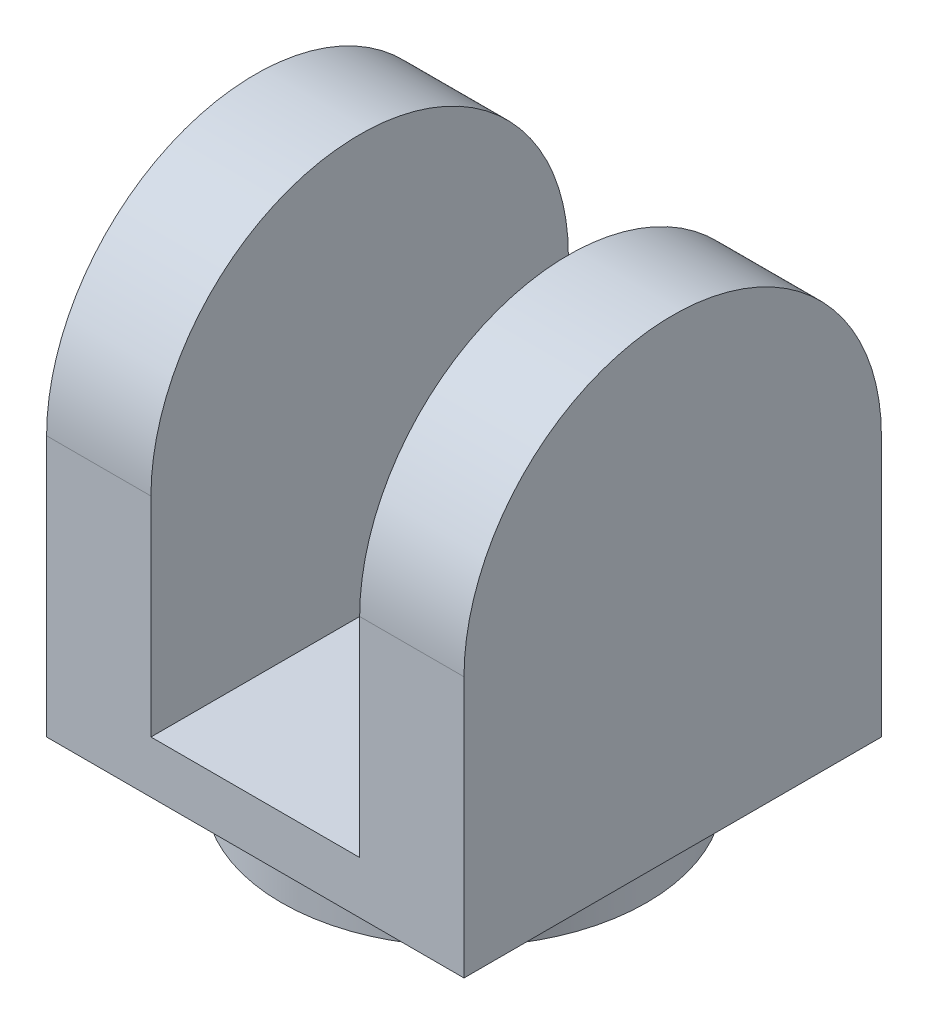
SolidWorks part; units mm, degrees
ref_plane "前视基准面" through (0, 0, 0) normal (0, 0, 1) x (1, 0, 0)
ref_plane "上视基准面" through (0, 0, 0) normal (0, 1, 0) x (1, 0, 0)
ref_plane "右视基准面" through (0, 0, 0) normal (1, 0, 0) x (0, 0, -1)
sketch "草图1" plane through (0, 0, 0) normal (0, 1, 0) x (1, 0, 0)
  circle A0 centre (0, 0) radius 7
extrude "凸台-拉伸1" add sketch "草图1" along normal blind 2
sketch "草图2" plane through (0, 2, 0) normal (0, 1, 0) x (1, 0, 0)
  line L0 (0, 0) -> (10.4307, 0) construction
  line L1 (-8, 8) -> (8, 8)
  line L2 (-8, 8) -> (-8, -8)
  line L3 (-8, -8) -> (8, -8)
  line L4 (8, 8) -> (8, -8)
  line L5 (0, 0) -> (0, -9.7125) construction
  dimension "D1" = 16
  dimension "D2" = 8
  dimension "D3" = 16
  dimension "D4" = 8
extrude "凸台-拉伸2" add sketch "草图2" along normal blind 18
sketch "草图3" plane through (0, 0, 8) normal (0, 0, 1) x (1, 0, 0)
  line L0 (-8, 20) -> (8, 20) construction
  line L1 (-4, 20) -> (4, 20)
  line L2 (-4, 20) -> (-4, 4)
  line L3 (-4, 4) -> (4, 4)
  line L4 (4, 20) -> (4, 4)
  dimension "D1" = 8
  dimension "D2" = 16
  dimension "D3" = 4
extrude "切除-拉伸1" cut sketch "草图3" against normal blind 16
sketch "草图4" plane through (8, 0, 0) normal (1, 0, 0) x (0, 0, -1)
  line L2 (-8, 12) -> (-8, 21.5579)
  line L3 (-8, 21.5579) -> (8, 21.5579)
  line L4 (8, 12) -> (8, 21.5579)
  arc A0 (8, 12) -> (-8, 12) centre (0, 12) ccw
extrude "切除-拉伸2" cut sketch "草图4" against normal blind 16
